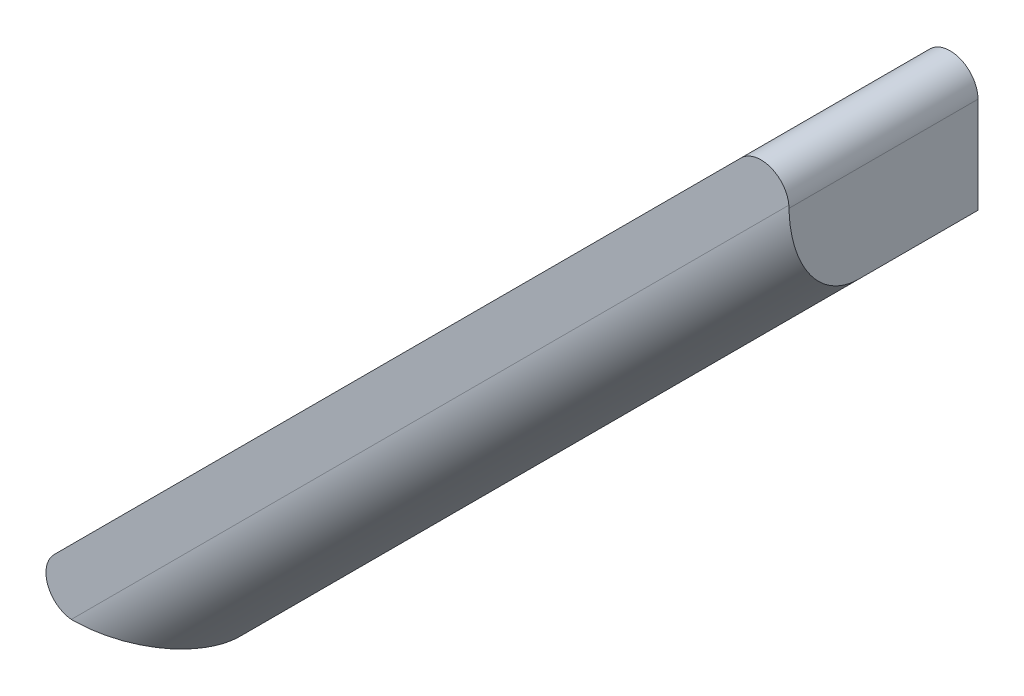
SolidWorks part; units mm, degrees
ref_plane "前视基准面" through (0, 0, 0) normal (0, 0, 1) x (1, 0, 0)
ref_plane "上视基准面" through (0, 0, 0) normal (0, 1, 0) x (1, 0, 0)
ref_plane "右视基准面" through (0, 0, 0) normal (1, 0, 0) x (0, 0, -1)
sketch "草图1" plane through (0, 0, 0) normal (0, 0, 1) x (1, 0, 0)
  line L0 (0, 0) -> (0, -11.7)
  line L1 (0, -11.7) -> (-44.1942, -55.8942)
  line L2 (-44.1942, -55.8942) -> (-55.8942, -55.8942)
  line L3 (-55.8942, -55.8942) -> (0, 0)
extrude "凸台-拉伸1" add sketch "草图1" along normal blind 13.5
fillet "圆角1" radius 2 1 edges at (-55.8942, -55.8942, 6.75)
fillet "圆角2" radius 2 1 edges at (0, 0, 6.75)
fillet "圆角3" radius 5 1 edges at (-22.0971, -33.7971, 13.5)
